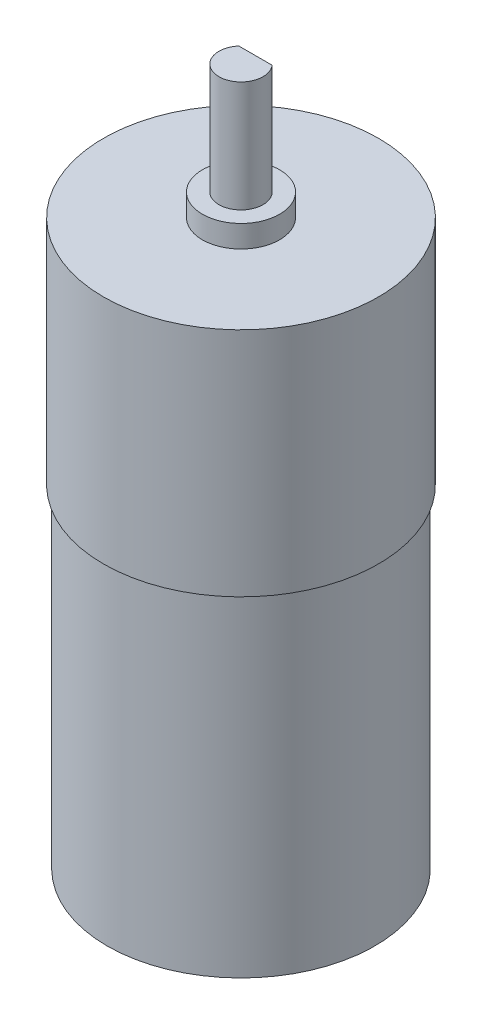
SolidWorks part; units mm, degrees
ref_plane "Front Plane" through (0, 0, 0) normal (0, 0, 1) x (1, 0, 0)
ref_plane "Top Plane" through (0, 0, 0) normal (0, 1, 0) x (1, 0, 0)
ref_plane "Right Plane" through (0, 0, 0) normal (1, 0, 0) x (0, 0, -1)
sketch "Sketch1" plane through (0, 0, 0) normal (1, 0, 0) x (0, 0, -1)
  line L0 (0, 44.2562) -> (0, -44.2562) construction
  line L2 (0, -31.8595) -> (12.075, -31.8595)
  line L3 (0, -31.8595) -> (0, -1.8595)
  line L4 (0, -1.8595) -> (12.075, -1.8595)
  line L5 (12.075, -31.8595) -> (12.075, -1.8595)
  dimension "D1" = 30
  dimension "D2" = 12.075
revolve "Revolve1" add sketch "Sketch1" angle 360 about L0
sketch "Sketch2" plane through (0, 0, 0) normal (1, 0, 0) x (0, 0, -1)
  line L0 (12.075, -1.8595) -> (-12.075, -1.8595) construction
  line L1 (0, -1.8595) -> (12.4, -1.8595)
  line L2 (0, -1.8595) -> (0, 19.0005)
  line L3 (0, 19.0005) -> (12.4, 19.0005)
  line L4 (12.4, -1.8595) -> (12.4, 19.0005)
  dimension "D1" = 20.86
  dimension "D2" = 12.4
revolve "Revolve2" add sketch "Sketch2" angle 360 about L2
sketch "Sketch3" plane through (0, 19.0005, 0) normal (0, 1, 0) x (1, 0, 0)
  circle A0 centre (0, 0) radius 3.48
  dimension "D1" = 6.96
extrude "Boss-Extrude1" add sketch "Sketch3" along normal blind 2
sketch "Sketch4" plane through (0, 21.0005, 0) normal (0, 1, 0) x (1, 0, 0)
  line L0 (-1.5, 1.3056) -> (1.5, 1.3056)
  arc A0 (-1.5, 1.3056) -> (1.5, 1.3056) centre (0, 0) ccw
  dimension "D1" = 3
extrude "Boss-Extrude2" add sketch "Sketch4" along normal blind 10
equation "\"D2@Sketch1\"=24.15/2"
equation "\"D2@Sketch2\"=24.8/2"
